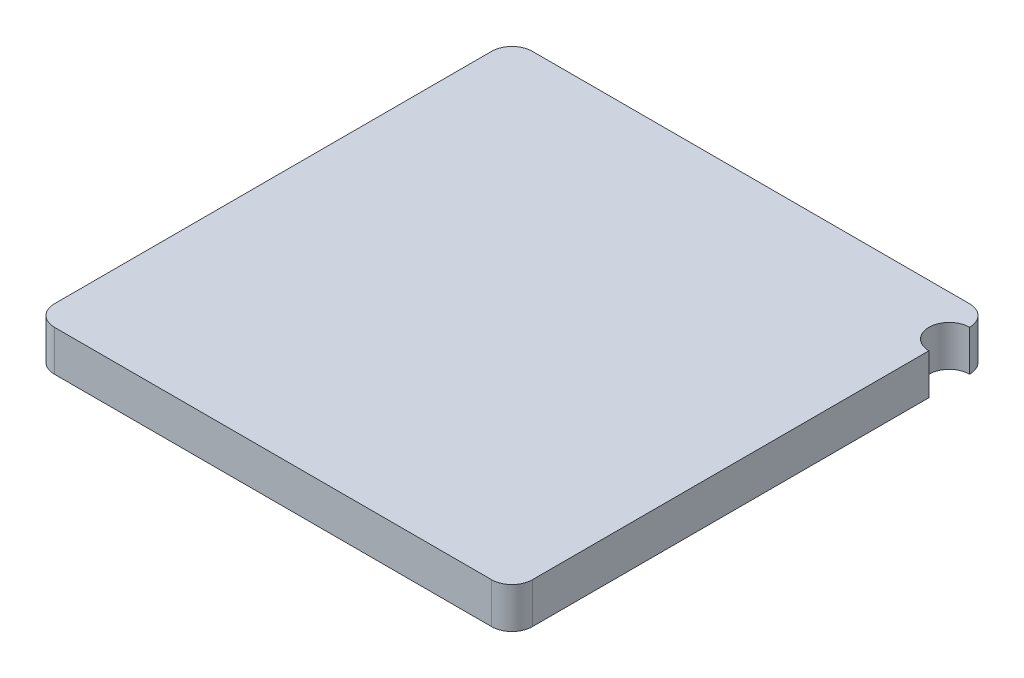
SolidWorks part; units mm, degrees
ref_plane "Front Plane" through (0, 0, 0) normal (0, 0, 1) x (1, 0, 0)
ref_plane "Top Plane" through (0, 0, 0) normal (0, 1, 0) x (1, 0, 0)
ref_plane "Right Plane" through (0, 0, 0) normal (1, 0, 0) x (0, 0, -1)
sketch "Sketch1" plane through (0, 0, 0) normal (0, 1, 0) x (1, 0, 0)
  line L1 (-1.175, 1.175) -> (1.175, 1.175)
  line L2 (-1.175, 1.175) -> (-1.175, -1.175)
  line L3 (-1.175, -1.175) -> (1.175, -1.175)
  line L4 (1.175, 1.175) -> (1.175, -1.175)
  line L5 (-1.175, 1.175) -> (1.175, -1.175) construction
  line L6 (-1.175, -1.175) -> (1.175, 1.175) construction
  point P0 (0, 0)
  dimension "D1" = 2.35
extrude "Boss-Extrude1" add sketch "Sketch1" along normal blind 0.2
fillet "Fillet1" radius 0.1 4 edges at (1.175, 0.1, 1.175) (-1.175, 0.1, 1.175) (1.175, 0.1, -1.175) (-1.175, 0.1, -1.175)
sketch "Sketch2" plane through (0, 0.2, 0) normal (0, 1, 0) x (1, 0, 0)
  line L0 (1.175, -1.075) -> (1.175, 1.075) construction
  line L1 (1.075, 1.175) -> (-1.075, 1.175) construction
  circle A0 centre (1.175, 0.975) radius 0.1
  dimension "D1" = 0.2
  dimension "D2" = 0.2
extrude "Cut-Extrude1" cut sketch "Sketch2" against normal through all
